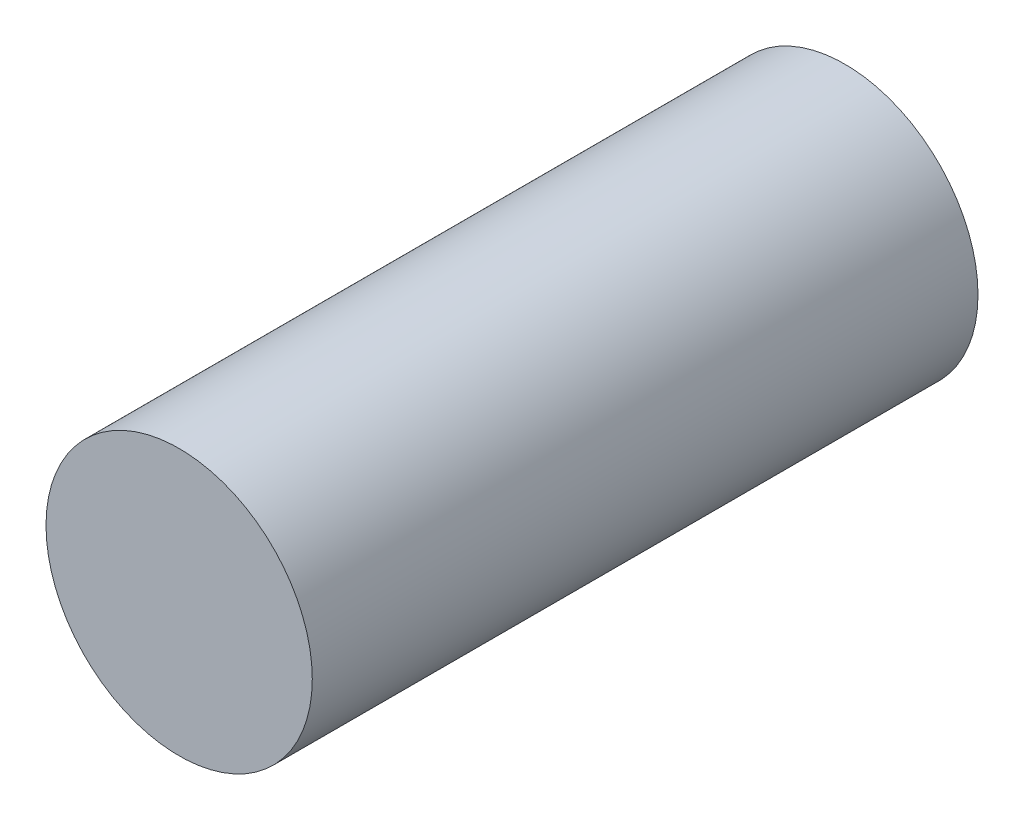
SolidWorks part; units mm, degrees
ref_plane "Front Plane" through (0, 0, 0) normal (0, 0, 1) x (1, 0, 0)
ref_plane "Top Plane" through (0, 0, 0) normal (0, 1, 0) x (1, 0, 0)
ref_plane "Right Plane" through (0, 0, 0) normal (1, 0, 0) x (0, 0, -1)
sketch "Sketch1" plane through (0, 0, 0) normal (0, 0, 1) x (1, 0, 0)
  circle A0 centre (0, 0) radius 25.4
  dimension "D1" = 50.8
extrude "Boss-Extrude1" add sketch "Sketch1" along normal blind 127
